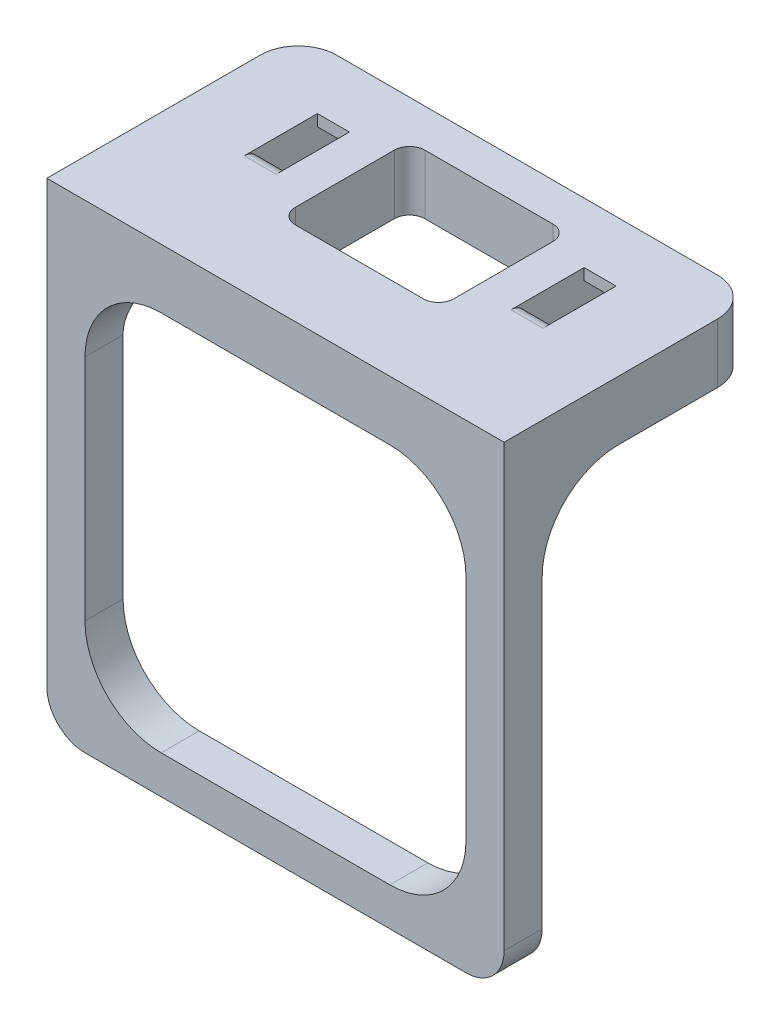
SolidWorks part; units mm, degrees
ref_plane "Front Plane" through (0, 0, 0) normal (0, 0, 1) x (1, 0, 0)
ref_plane "Top Plane" through (0, 0, 0) normal (0, 1, 0) x (1, 0, 0)
ref_plane "Right Plane" through (0, 0, 0) normal (1, 0, 0) x (0, 0, -1)
sketch "Sketch1" plane through (0, 0, 0) normal (0, 1, 0) x (1, 0, 0)
  line L1 (0, 33) -> (60, 33)
  line L2 (0, 33) -> (0, 0)
  line L3 (0, 0) -> (60, 0)
  line L4 (60, 33) -> (60, 0)
  dimension "D1" = 0
  dimension "D2" = 0
  dimension "D3" = 33
  dimension "D4" = 60
extrude "Boss-Extrude1" add sketch "Sketch1" along normal blind 10
sketch "Sketch2" plane through (0, 10, 0) normal (0, 1, 0) x (1, 0, 0)
  line L0 (30, 33) -> (30, 9.4174)
  line L1 (10.4, 28.5) -> (14.6, 28.5)
  line L2 (10.4, 28.5) -> (10.4, 17.5)
  line L3 (10.4, 17.5) -> (14.6, 17.5)
  line L4 (14.6, 28.5) -> (14.6, 17.5)
  line L5 (60, 33) -> (0, 33) construction
  line L6 (0, 0) -> (60, 0) construction
  line L7 (49.6, 17.5) -> (45.4, 17.5)
  line L8 (45.4, 28.5) -> (45.4, 17.5)
  line L9 (49.6, 28.5) -> (45.4, 28.5)
  line L10 (49.6, 28.5) -> (49.6, 17.5)
  dimension "D1" = 4.2
  dimension "D2" = 15.4
  dimension "D3" = 17.5
  dimension "D4" = 11
extrude "Cut-Extrude1" cut sketch "Sketch2" against normal blind 5.8 contours L4 L1 L2 L3 | L10 L9 L8 L7
sketch "Sketch3" plane through (14.6, 0, 0) normal (-1, 0, 0) x (0, 0, 1)
  line L0 (-28.5, 5.85) -> (-25.1, 8.5)
  line L1 (-28.5, 4.2) -> (-28.5, 10) construction
  line L2 (-25.1, 8.5) -> (-25.1, 10)
  line L3 (-28.5, 10) -> (-17.5, 10) construction
  line L4 (-28.5, 4.2) -> (-17.5, 4.2) construction
  line L5 (-28.5, 5.85) -> (-28.5, 10)
  line L6 (-28.5, 10) -> (-25.1, 10)
  dimension "D1" = 1.65
  dimension "D2" = 3.4
  dimension "D3" = 1.5
extrude "Boss-Extrude2" add sketch "Sketch3" along normal blind 55.8 from surface at -45.4 starting at face at (60, 5, -16.5)
sketch "Sketch4" plane through (60, 0, 0) normal (1, 0, 0) x (0, 0, -1)
  line L0 (33, 10) -> (33, 0) construction
  line L1 (0, 0) -> (33, 0)
  line L2 (0, 0) -> (0, 2.2)
  line L3 (0, 2.2) -> (33, 2.2)
  line L4 (33, 0) -> (33, 2.2)
  line L5 (28.5, 4.2) -> (17.5, 4.2) construction
  dimension "D1" = 2
extrude "Cut-Extrude2" cut sketch "Sketch4" against normal through all both and the other way through all
fillet "Fillet1" radius 2 2 edges at (47.5, 10, -17.5) (12.5, 10, -17.5)
sketch "Sketch5" plane through (0, 10, 0) normal (0, 1, 0) x (1, 0, 0)
  line L0 (60, 0) -> (60, 33) construction
  line L1 (0, 0) -> (60, 0)
  line L2 (0, 0) -> (0, 5)
  line L3 (0, 5) -> (60, 5)
  line L4 (60, 0) -> (60, 5)
  dimension "D1" = 5
sketch "Sketch7" plane through (0, 10, 0) normal (0, 1, 0) x (1, 0, 0)
  line L0 (14.6, 25.1) -> (14.6, 15.5) construction
  line L1 (19.6, 28) -> (40.4, 28)
  line L2 (19.6, 28) -> (19.6, 11)
  line L3 (19.6, 11) -> (40.4, 11)
  line L4 (40.4, 28) -> (40.4, 11)
  line L5 (45.4, 25.1) -> (45.4, 15.5) construction
  line L6 (60, 33) -> (0, 33) construction
  line L8 (0, 0) -> (60, 0) construction
  dimension "D1" = 5
  dimension "D2" = 5
  dimension "D3" = 5
  dimension "D4" = 11
extrude "Cut-Extrude4" cut sketch "Sketch7" against normal blind 16
fillet "Fillet2" radius 2 4 edges at (40.4, 6.1, -11) (19.6, 6.1, -11) (19.6, 6.1, -28) (40.4, 6.1, -28)
extrude "Boss-Extrude4" add sketch "Sketch5" against normal blind 55 from surface at -7.8 starting at face at (30, 2.2, -19.5)
sketch "Sketch8" plane through (0, 0, -5) normal (0, 0, -1) x (-1, 0, 0)
  line L0 (0, 10) -> (0, -52.8) construction
  line L1 (-55, -47.8) -> (-5, -47.8)
  line L2 (-55, -47.8) -> (-55, 2.2)
  line L3 (-55, 2.2) -> (-5, 2.2)
  line L4 (-5, -47.8) -> (-5, 2.2)
  line L5 (0, -52.8) -> (-60, -52.8) construction
  line L6 (-60, 10) -> (-60, -52.8) construction
  line L7 (-60, 2.2) -> (0, 2.2) construction
  dimension "D1" = 5
  dimension "D2" = 5
  dimension "D3" = 5
  dimension "D4" = 0
extrude "Cut-Extrude5" cut sketch "Sketch8" against normal blind 52.15
fillet "Fillet3" radius 10 6 edges at (5, -47.8, -2.5) (55, -47.8, -2.5) (57.5, 2.2, -5) (55, 2.2, -2.5) (2.5, 2.2, -5) (5, 2.2, -2.5)
fillet "Fillet4" radius 5 2 edges at (0, -52.8, -2.5) (60, -52.8, -2.5)
sketch "Sketch9" plane through (0, 0, 0) normal (0, 0, 1) x (1, 0, 0)
  line L3 (5, -37.8) -> (5, -7.8) construction
  line L4 (45, -47.8) -> (15, -47.8) construction
  circle A0 centre (28.575, -24.225) radius 20
  point P6 (0, 0)
  dimension "D3" = 40
  dimension "D1" = 23.575
  dimension "D2" = 23.575
sketch "Sketch10" plane through (0, 0, 0) normal (0, 0, 1) x (1, 0, 0)
  line L0 (5, -22.8) -> (55, -22.8)
  line L1 (5, -37.8) -> (5, -7.8) construction
  line L2 (55, -7.8) -> (55, -37.8) construction
fillet "Fillet6" radius 5 2 edges at (0, 6.1, -33) (60, 6.1, -33)
